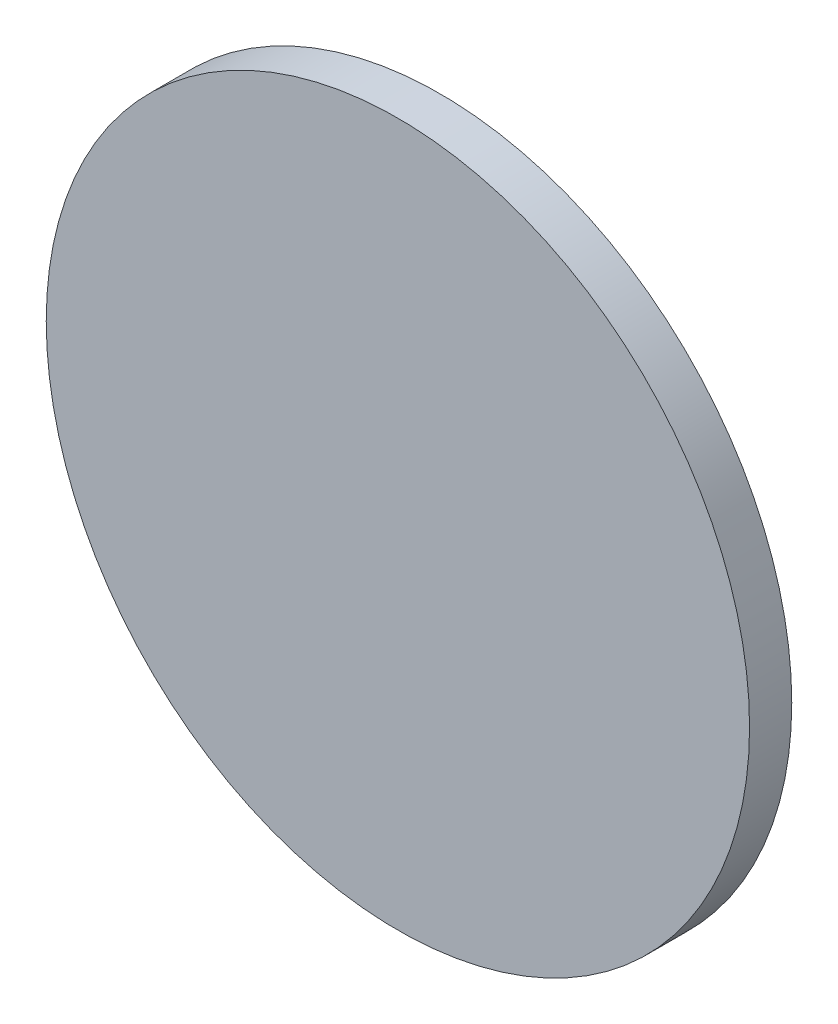
SolidWorks part; units mm, degrees
material "1023 Carbon Steel Sheet (SS)"
ref_plane "Front Plane" through (0, 0, 0) normal (0, 0, 1) x (1, 0, 0)
ref_plane "Top Plane" through (0, 0, 0) normal (0, 1, 0) x (1, 0, 0)
ref_plane "Right Plane" through (0, 0, 0) normal (1, 0, 0) x (0, 0, -1)
sketch "Sketch2" plane through (0, 0, 0) normal (0, 0, 1) x (1, 0, 0)
  circle A0 centre (0, 0) radius 25
extrude "Boss-Extrude1" add sketch "Sketch2" along normal blind 3
